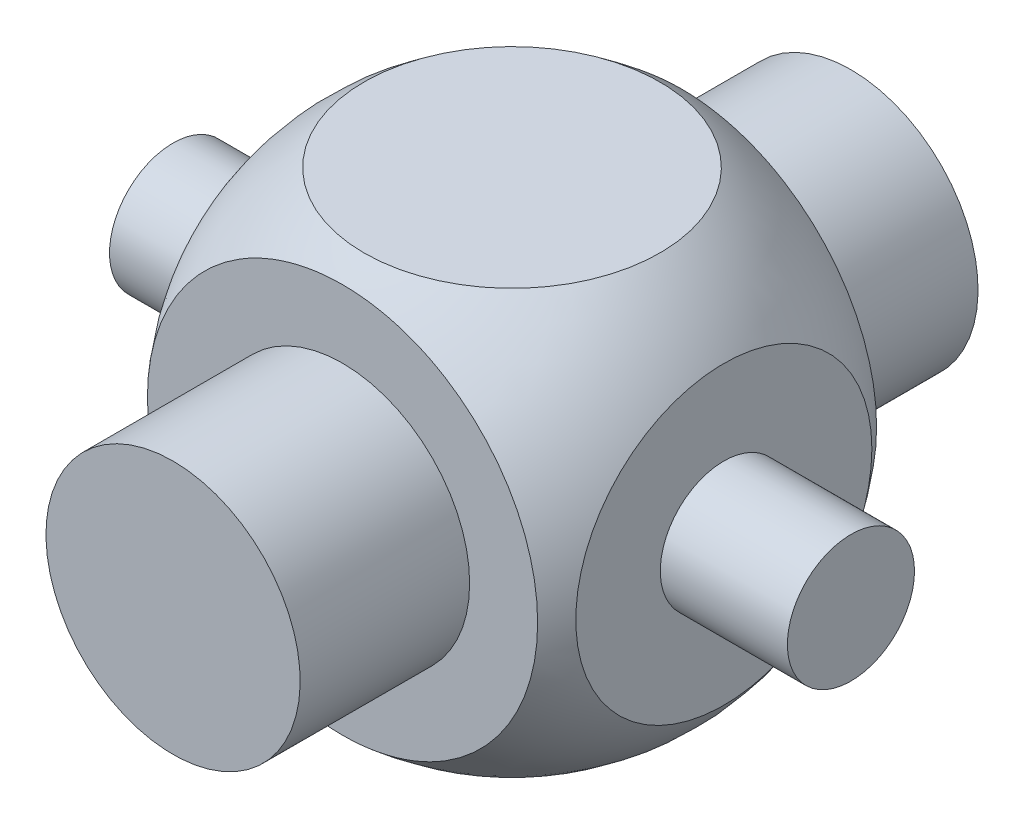
SolidWorks part; units mm, degrees
other "Markup1"
sketch "Sketch7" plane through (4, 1.05, 4) normal (0.6819, -0.3889, 0.6195) x (0.5453, -0.2943, -0.7849)
ref_plane "Ön Düzlem" through (0, 0, 0) normal (0, 0, 1) x (1, 0, 0)
ref_plane "Üst Düzlem" through (0, 0, 0) normal (0, 1, 0) x (1, 0, 0)
ref_plane "Sağ Düzlem" through (0, 0, 0) normal (1, 0, 0) x (0, 0, -1)
sketch "Sketch2" plane through (0, 0, 0) normal (1, 0, 0) x (0, 0, -1)
  line L0 (0, 0) -> (0, 6.1)
  arc A0 (0, 0) -> (0, 6.1) centre (0, 3.05) ccw
  dimension "D1" = 6.1
revolve "Revolve3" add sketch "Sketch2" angle 360 about L0
sketch "Sketch3" plane through (0, 0, 0) normal (1, 0, 0) x (0, 0, -1)
  line L0 (-3.05, 3.05) -> (3.05, 3.05) construction
  line L1 (-2, 5.55) -> (2, 5.55)
  line L2 (-2, 5.55) -> (-2, 0.55)
  line L3 (-2, 0.55) -> (2, 0.55)
  line L4 (2, 5.55) -> (2, 0.55)
  line L5 (-2, 5.55) -> (2, 0.55) construction
  line L6 (-2, 0.55) -> (2, 5.55) construction
  line L7 (0, 0) -> (0, 6.1) construction
  circle A0 centre (0, 3.05) radius 3.05 construction
  point P0 (0, 3.05)
  point P14 (0, 3.05)
  dimension "D1" = 4
  dimension "D2" = 5
extrude "Cut-Extrude1" cut sketch "Sketch3" against normal through all and the other way through all flip side to cut
sketch "Sketch4" plane through (0, 0, 0) normal (0, 0, 1) x (1, 0, 0)
  line L0 (0, 0.55) -> (0, 5.55) construction
  line L1 (-1.7471, 0.55) -> (1.7471, 0.55) construction
  line L2 (1.7471, 5.55) -> (-1.7471, 5.55) construction
  line L3 (-3.05, 3.05) -> (3.05, 3.05) construction
  line L5 (-2.5, 0.55) -> (2.5, 0.55)
  line L6 (-2.5, 0.55) -> (-2.5, 5.55)
  line L7 (-2.5, 5.55) -> (2.5, 5.55)
  line L8 (2.5, 0.55) -> (2.5, 5.55)
  line L9 (-2.5, 0.55) -> (2.5, 5.55) construction
  line L10 (-2.5, 5.55) -> (2.5, 0.55) construction
  arc A0 (-1.7471, 5.55) -> (-1.7471, 0.55) centre (0, 3.05) ccw construction
  arc A1 (1.7471, 0.55) -> (1.7471, 5.55) centre (0, 3.05) ccw construction
  point P14 (0, 3.05)
  dimension "D1" = 5
extrude "Cut-Extrude2" cut sketch "Sketch4" against normal through all and the other way through all flip side to cut
sketch "Sketch5" plane through (2.5, 0, 0) normal (1, 0, 0) x (0, 0, -1)
  circle A0 centre (0, 3.05) radius 0.75
  circle A1 centre (0, 3.05) radius 1.7471 construction
  dimension "D1" = 1.5
extrude "Boss-Extrude1" add sketch "Sketch5" along normal blind 1.5
mirror "Mirror1" about plane through (0, 0, 0) normal (1, 0, 0) of "Boss-Extrude1"
sketch "Sketch6" plane through (0, 0, -2) normal (0, 0, -1) x (-1, 0, 0)
  circle A0 centre (0, 3.05) radius 1.5
  circle A1 centre (0, 3.05) radius 2.3027 construction
  dimension "D1" = 3
extrude "Boss-Extrude2" add sketch "Sketch6" along normal blind 2
mirror "Mirror2" about plane through (0, 0, 0) normal (0, 0, 1) of "Boss-Extrude2"
